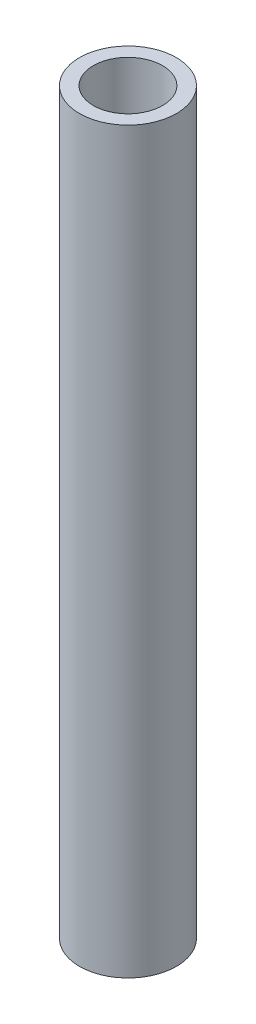
SolidWorks part; units mm, degrees
material "PVC Rigid"
ref_plane "Front Plane" through (0, 0, 0) normal (0, 0, 1) x (1, 0, 0)
ref_plane "Top Plane" through (0, 0, 0) normal (0, 1, 0) x (1, 0, 0)
ref_plane "Right Plane" through (0, 0, 0) normal (1, 0, 0) x (0, 0, -1)
sketch "Sketch5" plane through (0, 0, 0) normal (0, 1, 0) x (1, 0, 0)
  circle A0 centre (0, 0) radius 13.335
  circle A1 centre (0, 0) radius 9.525
  dimension "D1" = 26.67
  dimension "D2" = 19.05
extrude "Boss-Extrude1" add sketch "Sketch5" along normal blind 203.2
